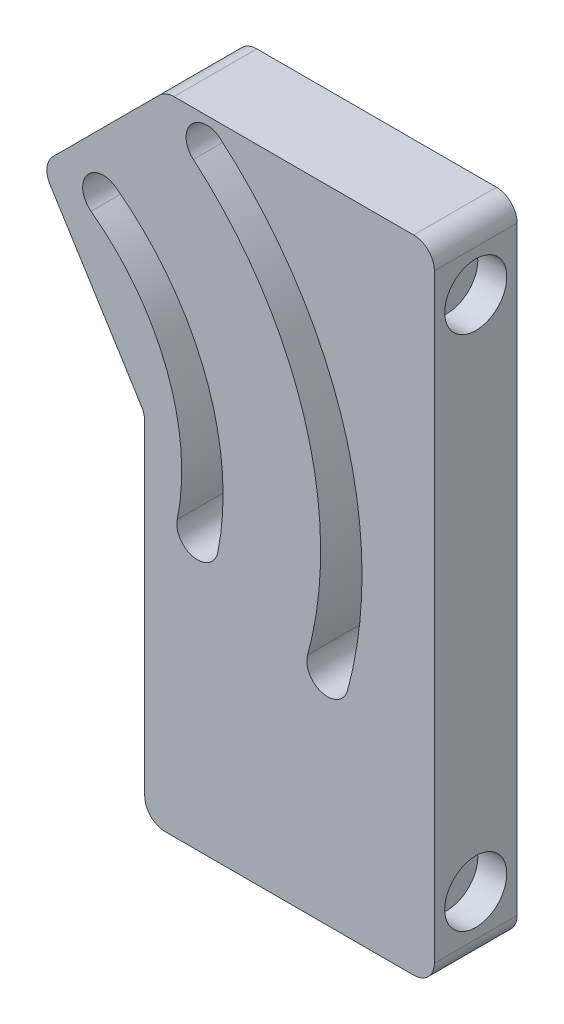
SolidWorks part; units mm, degrees
ref_plane "Front Plane" through (0, 0, 0) normal (0, 0, 1) x (1, 0, 0)
ref_plane "Top Plane" through (0, 0, 0) normal (0, 1, 0) x (1, 0, 0)
ref_plane "Right Plane" through (0, 0, 0) normal (1, 0, 0) x (0, 0, -1)
sketch "Sketch1" plane through (0, 0, 0) normal (0, 0, 1) x (1, 0, 0)
  line L0 (0, 0) -> (0, -196.7476)
  line L1 (0, -196.7476) -> (-88.9, -196.7476)
  line L2 (-88.9, -196.7476) -> (-120.65, -158.6476)
  line L3 (-120.65, -158.6476) -> (-120.65, -38.1)
  line L4 (-120.65, -38.1) -> (-82.55, 0)
  line L5 (-82.55, 0) -> (0, 0)
  point P0 (0, 0)
  dimension "D1" = 82.55
  dimension "D2" = 38.1
  dimension "D3" = 196.85
  dimension "D4" = 38.1
  dimension "D5" = 38.1
  dimension "D6" = 88.9
extrude "Boss-Extrude1" add sketch "Sketch1" along normal blind 25.4
sketch "Sketch2" plane through (0, 0, 0) normal (1, 0, 0) x (0, 0, -1)
  line L0 (-25.4, 0) -> (0, 0) construction
  line L1 (-25.4, -196.7476) -> (0, -196.7476) construction
  line L2 (-25.4, -196.7476) -> (-25.4, 0) construction
  circle A0 centre (-12.7, -19.05) radius 9.525
  circle A1 centre (-12.7, -177.6976) radius 9.525
  dimension "D1" = 19.05
  dimension "D2" = 19.05
  dimension "D3" = 19.05
  dimension "D4" = 19.05
  dimension "D5" = 12.7
  dimension "D6" = 12.7
extrude "Cut-Extrude1" cut sketch "Sketch2" against normal blind 8.89
sketch "Sketch3" plane through (0, 0, 25.4) normal (0, 0, 1) x (1, 0, 0)
  line L0 (-120.65, -38.1) -> (-120.65, -158.6476) construction
  line L1 (-88.9, -196.7476) -> (0, -196.7476) construction
  line L2 (0, 0) -> (-82.55, 0) construction
  arc A0 (-101.6, -38.1) -> (-72.6844, -113.1568) centre (-146.05, -98.3226) cw construction
  arc A5 (-66.4604, -114.4153) -> (-97.829, -32.991) centre (-146.05, -98.3226) ccw
  arc A10 (-78.9085, -111.8983) -> (-105.371, -43.209) centre (-146.05, -98.3226) ccw
  arc A11 (-78.9085, -111.8983) -> (-66.4604, -114.4153) centre (-72.6844, -113.1568) ccw
  arc A12 (-97.829, -32.991) -> (-105.371, -43.209) centre (-101.6, -38.1) ccw
  arc A13 (-69.85, -8.89) -> (-32.7931, -129.5874) centre (-146.05, -98.3226) cw construction
  arc A14 (-26.672, -131.2771) -> (-65.7317, -4.0566) centre (-146.05, -98.3226) ccw
  arc A15 (-38.9141, -127.8976) -> (-73.9683, -13.7234) centre (-146.05, -98.3226) ccw
  arc A16 (-38.9141, -127.8976) -> (-26.672, -131.2771) centre (-32.7931, -129.5874) ccw
  arc A17 (-65.7317, -4.0566) -> (-73.9683, -13.7234) centre (-69.85, -8.89) ccw
  point P0 (-146.05, -98.3226)
  point P4 (-76.2037, -71.4143)
  point P9 (-33.7315, -63.8381)
  point P17 (0, 0)
  point P22 (0, 0)
  point P23 (-89.5113, -74.542)
  point P24 (0, 0)
  point P25 (0, 0)
  point P26 (-86.6231, -79.8372)
  point P27 (-38.3317, -63.6329)
  point P28 (3.4214, -128.8087)
  point P29 (-70.9117, -81.4664)
  point P32 (-85.3288, -38.1)
  point P33 (-54.716, -8.89)
  point P34 (-60.8227, -69.0579)
  dimension "D5" = 8.89
  dimension "D4" = 38.1
  dimension "D6" = 6.35
  dimension "D8" = 6.35
  dimension "D1" = 98.425
  dimension "D2" = 65
  dimension "D3" = 65
  dimension "D7" = 25.4
  dimension "D9" = 44.45
  dimension "D10" = 76.2
extrude "Cut-Extrude2" cut sketch "Sketch3" against normal through all
sketch "Sketch4" plane through (0, 0, 25.4) normal (0, 0, 1) x (1, 0, 0)
  line L0 (-120.65, -38.1) -> (-88.9, -88.9)
  line L4 (-88.9, -88.9) -> (-88.9, -196.7476)
  line L5 (-88.9, -196.7476) -> (-120.65, -158.6476)
  line L6 (-120.65, -158.6476) -> (-120.65, -38.1)
  dimension "D1" = 50.8
extrude "Cut-Extrude3" cut sketch "Sketch4" against normal through all
fillet "Fillet1" radius 6.35 6 edges at (-88.9, -88.9, 12.7) (-120.65, -38.1, 12.7) (-82.55, 0, 12.7) (0, 0, 12.7) (0, -196.7476, 12.7) (-88.9, -196.7476, 12.7)
